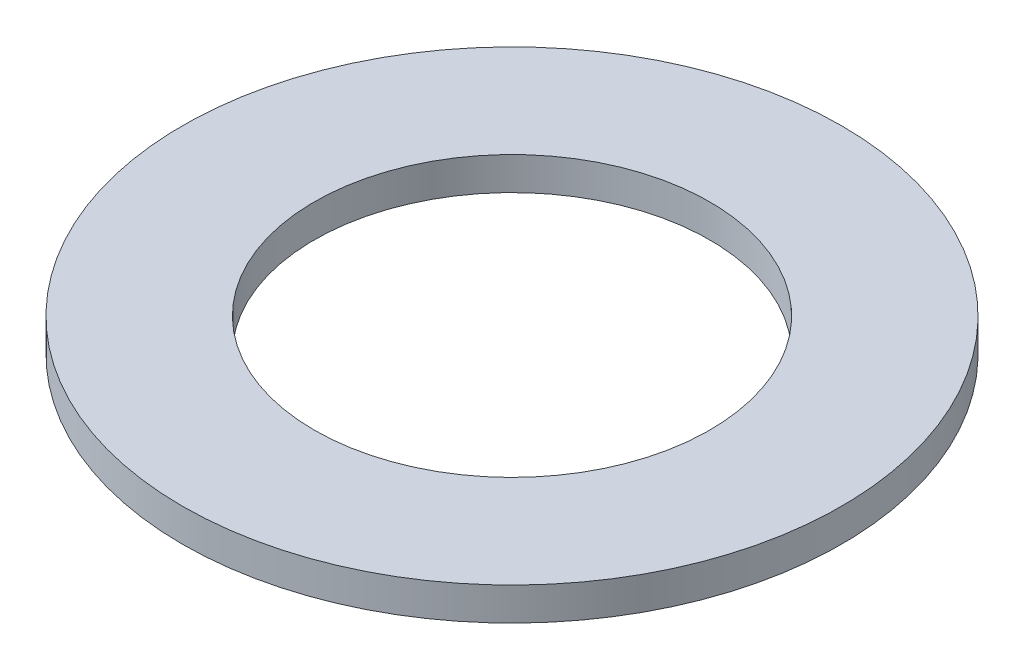
SolidWorks part; units mm, degrees
ref_plane "Front Plane" through (0, 0, 0) normal (0, 0, 1) x (1, 0, 0)
ref_plane "Top Plane" through (0, 0, 0) normal (0, 1, 0) x (1, 0, 0)
ref_plane "Right Plane" through (0, 0, 0) normal (1, 0, 0) x (0, 0, -1)
sketch "Sketch1" plane through (0, 0, 0) normal (0, 1, 0) x (1, 0, 0)
  circle A0 centre (0, 0) radius 5
  circle A1 centre (0, 0) radius 3
  circle A2 centre (0, 0) radius 3.25 construction
  dimension "D1" = 10
  dimension "D2" = 2
  dimension "D3" = 0.25
sketch "Sketch4" plane through (0, 0, 0) normal (0, 1, 0) x (1, 0, 0)
  line L0 (-1.2714, 2.991) -> (-4.5992, 1.3737) construction
  line L1 (-1.2277, 2.901) -> (-4.5555, 1.2838)
  line L2 (-1.3151, 3.0809) -> (-4.6429, 1.4636)
  line L3 (0.3961, 3.228) -> (-3.2945, 3.4913) construction
  line L4 (0.389, 3.1283) -> (-3.3016, 3.3916)
  line L5 (0.4032, 3.3278) -> (-3.2874, 3.5911)
  line L6 (1.9588, 2.5996) -> (-1.1058, 4.6729) construction
  line L7 (1.9027, 2.5168) -> (-1.1618, 4.5901)
  line L8 (2.0148, 2.6824) -> (-1.0497, 4.7557)
  line L9 (2.9978, 1.274) -> (1.3805, 4.6018) construction
  line L10 (2.9079, 1.2303) -> (1.2906, 4.5581)
  line L11 (3.0878, 1.3177) -> (1.4705, 4.6455)
  line L12 (3.2349, -0.3935) -> (3.4982, 3.2971) construction
  line L13 (3.1351, -0.3864) -> (3.3984, 3.3042)
  line L14 (3.3346, -0.4006) -> (3.5979, 3.29)
  line L15 (2.6064, -1.9562) -> (4.6797, 1.1084) construction
  line L16 (2.5236, -1.9001) -> (4.5969, 1.1644)
  line L17 (2.6892, -2.0122) -> (4.7626, 1.0523)
  line L18 (1.2808, -2.9952) -> (4.6086, -1.3779) construction
  line L19 (1.2371, -2.9053) -> (4.5649, -1.288)
  line L20 (1.3245, -3.0852) -> (4.6524, -1.4679)
  line L21 (-0.3867, -3.2323) -> (3.3039, -3.4956) construction
  line L22 (-0.3796, -3.1325) -> (3.311, -3.3958)
  line L23 (-0.3938, -3.332) -> (3.2968, -3.5953)
  line L24 (-1.9493, -2.6038) -> (1.1152, -4.6772) construction
  line L25 (-1.8933, -2.521) -> (1.1712, -4.5943)
  line L26 (-2.0054, -2.6867) -> (1.0591, -4.76)
  line L27 (-2.9884, -1.2782) -> (-1.3711, -4.6061) construction
  line L28 (-2.8985, -1.2345) -> (-1.2812, -4.5624)
  line L29 (-3.0783, -1.322) -> (-1.4611, -4.6498)
  line L30 (-3.2255, 0.3893) -> (-3.4888, -3.3013) construction
  line L31 (-3.1257, 0.3822) -> (-3.389, -3.3085)
  line L32 (-3.3252, 0.3964) -> (-3.5885, -3.2942)
  line L33 (-2.597, 1.9519) -> (-4.6703, -1.1126) construction
  line L34 (-2.5142, 1.8959) -> (-4.5875, -1.1686)
  line L35 (-2.6798, 2.008) -> (-4.7532, -1.0566)
  circle A0 centre (0, 0) radius 3.25 construction
  arc A1 (-1.2277, 2.901) -> (-1.3151, 3.0809) centre (-1.2714, 2.991) ccw
  arc A2 (-4.6429, 1.4636) -> (-4.5555, 1.2838) centre (-4.5992, 1.3737) ccw
  arc A3 (0.389, 3.1283) -> (0.4032, 3.3278) centre (0.3961, 3.228) ccw
  arc A4 (-3.2874, 3.5911) -> (-3.3016, 3.3916) centre (-3.2945, 3.4913) ccw
  arc A5 (1.9027, 2.5168) -> (2.0148, 2.6824) centre (1.9588, 2.5996) ccw
  arc A6 (-1.0497, 4.7557) -> (-1.1618, 4.5901) centre (-1.1058, 4.6729) ccw
  arc A7 (2.9079, 1.2303) -> (3.0878, 1.3177) centre (2.9978, 1.274) ccw
  arc A8 (1.4705, 4.6455) -> (1.2906, 4.5581) centre (1.3805, 4.6018) ccw
  arc A9 (3.1351, -0.3864) -> (3.3346, -0.4006) centre (3.2349, -0.3935) ccw
  arc A10 (3.5979, 3.29) -> (3.3984, 3.3042) centre (3.4982, 3.2971) ccw
  arc A11 (2.5236, -1.9001) -> (2.6892, -2.0122) centre (2.6064, -1.9562) ccw
  arc A12 (4.7626, 1.0523) -> (4.5969, 1.1644) centre (4.6797, 1.1084) ccw
  arc A13 (1.2371, -2.9053) -> (1.3245, -3.0852) centre (1.2808, -2.9952) ccw
  arc A14 (4.6524, -1.4679) -> (4.5649, -1.288) centre (4.6086, -1.3779) ccw
  arc A15 (-0.3796, -3.1325) -> (-0.3938, -3.332) centre (-0.3867, -3.2323) ccw
  arc A16 (3.2968, -3.5953) -> (3.311, -3.3958) centre (3.3039, -3.4956) ccw
  arc A17 (-1.8933, -2.521) -> (-2.0054, -2.6867) centre (-1.9493, -2.6038) ccw
  arc A18 (1.0591, -4.76) -> (1.1712, -4.5943) centre (1.1152, -4.6772) ccw
  arc A19 (-2.8985, -1.2345) -> (-3.0783, -1.322) centre (-2.9884, -1.2782) ccw
  arc A20 (-1.4611, -4.6498) -> (-1.2812, -4.5624) centre (-1.3711, -4.6061) ccw
  arc A21 (-3.1257, 0.3822) -> (-3.3252, 0.3964) centre (-3.2255, 0.3893) ccw
  arc A22 (-3.5885, -3.2942) -> (-3.389, -3.3085) centre (-3.4888, -3.3013) ccw
  arc A23 (-2.5142, 1.8959) -> (-2.6798, 2.008) centre (-2.597, 1.9519) ccw
  arc A24 (-4.7532, -1.0566) -> (-4.5875, -1.1686) centre (-4.6703, -1.1126) ccw
  point P4 (-2.9353, 2.1823)
  point P9 (1.9027, 2.5168)
  point P15 (-1.4492, 3.3597)
  point P22 (0.4265, 3.6363)
  point P29 (2.1892, 2.9379)
  point P36 (3.3665, 1.4518)
  point P43 (3.6431, -0.4239)
  point P50 (2.9447, -2.1866)
  point P57 (1.4586, -3.3639)
  point P64 (-0.4171, -3.6405)
  point P71 (-2.1798, -2.9422)
  point P78 (-3.3571, -1.456)
  point P85 (-3.6337, 0.4197)
  point P90 (0.0047, -0.0021)
  dimension "D1" = 0.2
  dimension "D2" = 3.7
  dimension "D3" = 4.8
  dimension "D4" = 12
extrude "Boss-Extrude2" add sketch "Sketch1" along normal blind 0.5
extrude "Cut-Extrude5" cut sketch "Sketch4" along normal blind 0.2 contours L1 A2 L2 A1 | L8 A6 L7 A5 | L11 A8 L10 A7 | L20 A14 L19 A13 | L29 A20 L28 A19 | L25 A18 L26 A17 | L32 A22 L31 A21 | L5 A4 L4 A3 | L35 A24 L34 A23 | L13 A10 L14 A9 | L16 A12 L17 A11 | L22 A16 L23 A15
